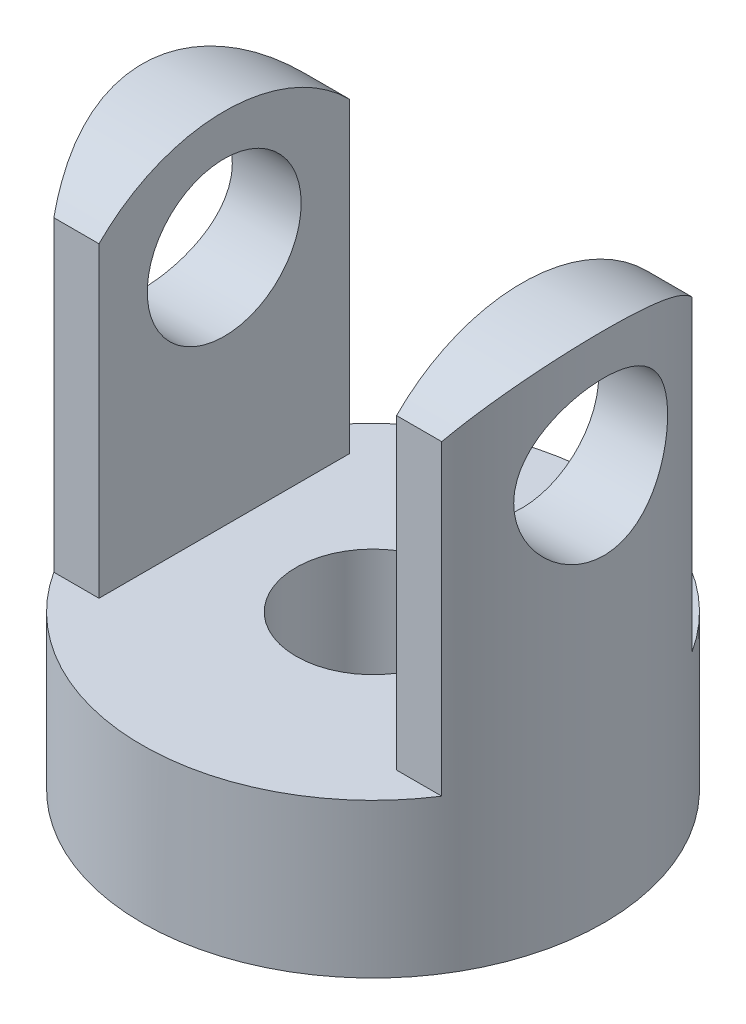
SolidWorks part; units mm, degrees
ref_plane "Front Plane" through (0, 0, 0) normal (0, 0, 1) x (1, 0, 0)
ref_plane "Top Plane" through (0, 0, 0) normal (0, 1, 0) x (1, 0, 0)
ref_plane "Right Plane" through (0, 0, 0) normal (1, 0, 0) x (0, 0, -1)
sketch "Sketch1" plane through (0, 0, 0) normal (0, 1, 0) x (1, 0, 0)
  circle A0 centre (0, 0) radius 4.5
  circle A1 centre (0, 0) radius 1.5
  dimension "D1" = 9
  dimension "D2" = 3
extrude "Boss-Extrude1" add sketch "Sketch1" along normal blind 3
sketch "Sketch2" plane through (0, 3, 0) normal (0, 1, 0) x (1, 0, 0)
  line L0 (-4.5, 0) -> (-2.9, 0) construction
  line L1 (0, -4.5) -> (0, 4.5) construction
  line L2 (-2.9, -3.4409) -> (-2.9, 3.4409)
  line L3 (2.9, -3.4409) -> (2.9, 3.4409)
  circle A0 centre (0, 0) radius 4.5 construction
  arc A1 (-2.9, -3.4409) -> (-2.798, 3.5244) centre (0, 0) cw
  arc A2 (2.9, -3.4409) -> (2.798, 3.5244) centre (0, 0) ccw
  point P11 (-2.9, 0)
  circle M4 centre (0, 0) radius 4.5
  dimension "D1" = 1.6
extrude "Boss-Extrude2" add sketch "Sketch2" along normal blind 7 contours L2 M4 | L3 M4
sketch "Sketch3" plane through (-2.9, 0, 0) normal (1, 0, 0) x (0, 0, -1)
  line L0 (3.4409, 10) -> (3.4409, 3) construction
  line L1 (-3.4409, 10) -> (-3.4409, 3) construction
  line L2 (3.4409, 6.5591) -> (3.4409, 10)
  line L3 (3.4409, 10) -> (-3.4409, 10)
  line L4 (-3.4409, 10) -> (-3.4409, 6.5591)
  line L5 (2.4409, 10) -> (2.4409, 3)
  line L6 (-3.4409, 3) -> (3.4409, 3) construction
  line L7 (-2.4409, 10) -> (-2.4409, 3)
  line L8 (3.4409, 10) -> (3.4409, 3)
  line L9 (-3.4409, 10) -> (-3.4409, 3)
  line L10 (-3.4409, 3) -> (3.4409, 3)
  arc A0 (3.4409, 6.5591) -> (-3.4409, 6.5591) centre (0, 6.5591) ccw
  circle A1 centre (0, 6.5591) radius 1.5 construction
  circle A2 centre (0, 7.7) radius 1.5
  line M1 (-3.4409, 3) -> (3.4409, 3)
  line M2 (3.4409, 3) -> (3.4409, 10)
  line M3 (3.4409, 10) -> (-3.4409, 10)
  line M4 (-3.4409, 10) -> (-3.4409, 3)
  dimension "D1" = 3
  dimension "D2" = 3
  dimension "D3" = 2.3
  dimension "D4" = 1
  dimension "D5" = 1
extrude "Cut-Extrude1" cut sketch "Sketch3" against normal blind 6.5 contours A0 M2 M3 | A0 L3 M4 | A1 | A2 | A0 L7 M3 | A0 L5 L3 | A0 L5 M2 M1 | L7 A0 M4 M1
mirror "Mirror1" about plane through (0, 0, 0) normal (1, 0, 0) of "Cut-Extrude1"
